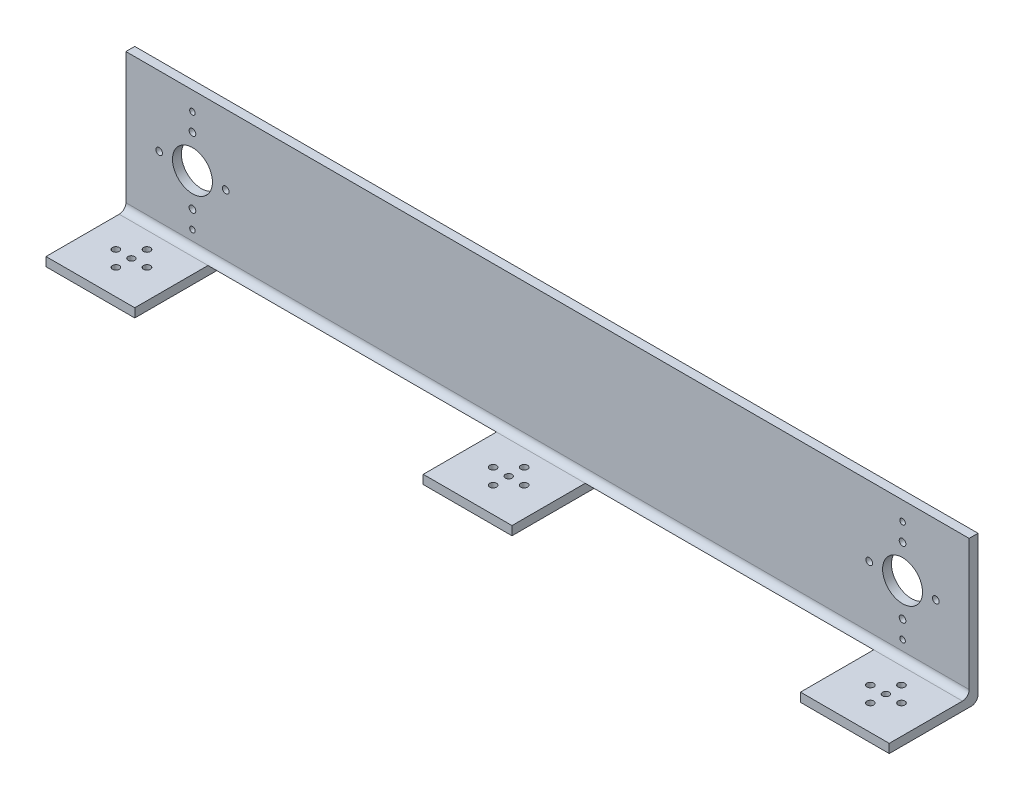
SolidWorks part; units mm, degrees
ref_plane "Front Plane" through (0, 0, 0) normal (0, 0, 1) x (1, 0, 0)
ref_plane "Top Plane" through (0, 0, 0) normal (0, 1, 0) x (1, 0, 0)
ref_plane "Right Plane" through (0, 0, 0) normal (1, 0, 0) x (0, 0, -1)
sketch "Sketch1" plane through (0, 0, 0) normal (1, 0, 0) x (0, 0, -1)
  line L0 (-32.2168, -27.7192) -> (7.7832, -27.7192)
  line L1 (7.7832, -27.7192) -> (7.7832, 38.2808)
  line L2 (-32.2168, -23.7192) -> (3.7832, -23.7192)
  line L3 (3.7832, -23.7192) -> (3.7832, 38.2808)
  line L4 (-32.2168, -23.7192) -> (-32.2168, -27.7192)
  line L5 (3.7832, 38.2808) -> (7.7832, 38.2808)
  dimension "D1" = 4
  dimension "D2" = 66
extrude "Boss-Extrude1" add sketch "Sketch1" along normal blind 380
fillet "Fillet4" radius 3 2 edges at (190, -23.7192, -3.7832) (190, -27.7192, -7.7832)
hole_wizard "Hole2" positions "Sketch7" profile "Sketch6" legacy
sketch "Sketch7" plane through (0, 0, -3.7832) normal (0, 0, 1) x (1, 0, 0)
  line L0 (380, 38.2808) -> (380, -20.7192) construction
  line L1 (380, 38.2808) -> (0, 38.2808) construction
  point P0 (30, 6.7808)
  point P2 (350, 6.7808)
  point P7 (380, 8.7808)
  dimension "D1" = 30
  dimension "D2" = 30
  dimension "D3" = 31.5
  dimension "D4" = 31.5
sketch "Sketch6" plane through (30, 6.7808, -3.7832) normal (1, 0, 0) x (0, -1, 0)
  line L0 (0, 0) -> (0, 4)
  line L1 (0, 4) -> (9, 4)
  line L2 (9, 4) -> (9, 0)
  line L3 (9, 0) -> (0, 0)
  line L4 (0, 110) -> (0, -10) construction
  dimension "Diameter" = 18
  dimension "Depth" = 4
sketch "Sketch18" plane through (0, -27.7192, 0) normal (0, -1, 0) x (1, 0, 0)
  line L0 (380, 32.2168) -> (0, 32.2168) construction
  line L1 (0, -4.7832) -> (380, -4.7832) construction
  line L2 (40, 32.2168) -> (170, 32.2168)
  line L3 (40, 32.2168) -> (40, -4.7832)
  line L4 (40, -4.7832) -> (170, -4.7832)
  line L5 (170, 32.2168) -> (170, -4.7832)
  line L7 (210, 32.2168) -> (340, 32.2168)
  line L8 (210, 32.2168) -> (210, -4.7832)
  line L9 (210, -4.7832) -> (340, -4.7832)
  line L10 (340, 32.2168) -> (340, -4.7832)
  dimension "D1" = 40
  dimension "D2" = 130
  dimension "D3" = 40
  dimension "D4" = 130
extrude "Cut-Extrude1" cut sketch "Sketch18" against normal blind 4
hole_wizard "Hole5" positions "3DSketch4" profile "Sketch23" legacy
sketch3d "3DSketch4"
  line L0 (340, -27.7192, -4.7832) -> (340, -27.7192, 32.2168) construction
  line L1 (380, -27.7192, 32.2168) -> (340, -27.7192, 32.2168) construction
  line L2 (170, -27.7192, -4.7832) -> (170, -27.7192, 32.2168) construction
  line L3 (210, -27.7192, 32.2168) -> (170, -27.7192, 32.2168) construction
  line L4 (0, -27.7192, 32.2168) -> (0, -27.7192, -4.7832) construction
  line L5 (40, -27.7192, 32.2168) -> (0, -27.7192, 32.2168) construction
  line L6 (20, -27.7192, 13.7168) -> (20, -27.7192, 32.7013)
  point P0 (360, -27.7192, 13.7168)
  point P2 (190, -27.7192, 13.7168)
  point P4 (20, -27.7192, 13.7168)
  dimension "D1" = 20
  dimension "D2" = 18.5
  dimension "D3" = 20
  dimension "D4" = 18.5
  dimension "D5" = 20
  dimension "D6" = 18.5
sketch "Sketch23" plane through (360, -27.7192, 13.7168) normal (1, 0, 0) x (0, 0, -1)
  line L0 (0, 0) -> (0, 4)
  line L1 (0, 4) -> (1.5, 4)
  line L2 (1.5, 4) -> (1.5, 0)
  line L3 (1.5, 0) -> (0, 0)
  line L4 (0, 110) -> (0, -10) construction
  dimension "Diameter" = 3
  dimension "Depth" = 4
hole_wizard "Hole6" positions "3DSketch5" profile "Sketch24" legacy
sketch3d "3DSketch5"
  line L0 (0, -24.7192, -7.7832) -> (0, 38.2808, -7.7832) construction
  line L1 (380, 38.2808, -7.7832) -> (0, 38.2808, -7.7832) construction
  line L3 (380, -24.7192, -7.7832) -> (380, 38.2808, -7.7832) construction
  circle A0 centre (30, 6.7808, -7.7832) radius 9 construction
  circle A1 centre (350, 6.7808, -7.7832) radius 9 construction
  point P0 (30, 21.7808, -7.7832)
  point P2 (15, 6.7808, -7.7832)
  point P4 (30, -8.2192, -7.7832)
  point P5 (350, -8.2192, -7.7832)
  point P7 (365, 6.7808, -7.7832)
  point P9 (350, 21.7808, -7.7832)
  point P11 (335, 6.7808, -7.7832)
  point P17 (45, 6.7808, -7.7832)
  point P20 (30, 6.7808, 1.2168)
  point P32 (350, 6.7808, 1.2168)
  dimension "D1" = 15
  dimension "D3" = 30
  dimension "D4" = 15
  dimension "D2" = 30
  dimension "D5" = 15
  dimension "D6" = 31.5
  dimension "D7" = 31.5
  dimension "D8" = 15
  dimension "D9" = 15
  dimension "D10" = 30
  dimension "D11" = 15
  dimension "D12" = 15
  dimension "D13" = 15
  dimension "D14" = 31.5
  dimension "D15" = 31.5
  dimension "D16" = 30
sketch "Sketch24" plane through (30, 21.7808, -7.7832) normal (1, 0, 0) x (0, 1, 0)
  line L0 (0, 0) -> (0, 4)
  line L1 (0, 4) -> (1.5, 4)
  line L2 (1.5, 4) -> (1.5, 0)
  line L3 (1.5, 0) -> (0, 0)
  line L4 (0, 110) -> (0, -10) construction
  dimension "Diameter" = 3
  dimension "Depth" = 4
hole_wizard "Hole7" positions "3DSketch6" profile "Sketch25" legacy
sketch3d "3DSketch6"
  line L0 (0, -24.7192, -7.7832) -> (0, 38.2808, -7.7832) construction
  line L1 (380, -24.7192, -7.7832) -> (380, 38.2808, -7.7832) construction
  circle A0 centre (30, 6.7808, -7.7832) radius 9 construction
  circle A1 centre (350, 6.7808, -7.7832) radius 9 construction
  point P0 (30, 29.7808, -7.7832)
  point P2 (30, -16.2192, -7.7832)
  point P4 (350, 29.7808, -7.7832)
  point P6 (350, -16.2192, -7.7832)
  point P11 (30, 6.7808, 1.2168)
  point P16 (350, 6.7808, 1.2168)
  dimension "D1" = 23
  dimension "D2" = 23
  dimension "D3" = 30
  dimension "D4" = 30
  dimension "D5" = 23
  dimension "D6" = 30
  dimension "D7" = 23
  dimension "D8" = 30
sketch "Sketch25" plane through (30, 29.7808, -7.7832) normal (1, 0, 0) x (0, 1, 0)
  line L0 (0, 0) -> (0, 4)
  line L1 (0, 4) -> (1.25, 4)
  line L2 (1.25, 4) -> (1.25, 0)
  line L3 (1.25, 0) -> (0, 0)
  line L4 (0, 110) -> (0, -10) construction
  dimension "Diameter" = 2.5
  dimension "Depth" = 4
sketch "Sketch27" plane through (0, -23.7192, 0) normal (0, 1, 0) x (1, 0, 0)
  line L0 (20, -13.7168) -> (20, -32.2168)
  line L1 (190, -13.7168) -> (190, -32.2168)
  line L3 (360, -13.7168) -> (360, -32.2168)
  circle A0 centre (20, -20.7168) radius 1.55
  circle A1 centre (20, -13.7168) radius 1.5 construction
  circle A2 centre (13, -13.7168) radius 1.55
  circle A3 centre (20, -6.7168) radius 1.55
  circle A4 centre (27, -13.7168) radius 1.55
  circle A5 centre (360, -20.7168) radius 1.55
  circle A6 centre (360, -13.7168) radius 1.5 construction
  circle A7 centre (353, -13.7168) radius 1.55
  circle A8 centre (360, -6.7168) radius 1.55
  circle A9 centre (367, -13.7168) radius 1.55
  circle A10 centre (190, -20.7168) radius 1.55
  circle A11 centre (190, -13.7168) radius 1.5 construction
  circle A12 centre (183, -13.7168) radius 1.55
  circle A13 centre (190, -6.7168) radius 1.55
  circle A14 centre (197, -13.7168) radius 1.55
  point P15 (20, -13.7168)
  point P30 (360, -13.7168)
  point P41 (190, -13.7168)
  dimension "D1" = 7
  dimension "D2" = 3.1
  dimension "D4" = 7
  dimension "D5" = 3.1
  dimension "D8" = 7
  dimension "D9" = 3.1
  dimension "D7" = 7
  dimension "D11" = 7
  dimension "D3" = 4
  dimension "D6" = 4
  dimension "D10" = 4
extrude "Cut-Extrude3" cut sketch "Sketch27" against normal blind 4
